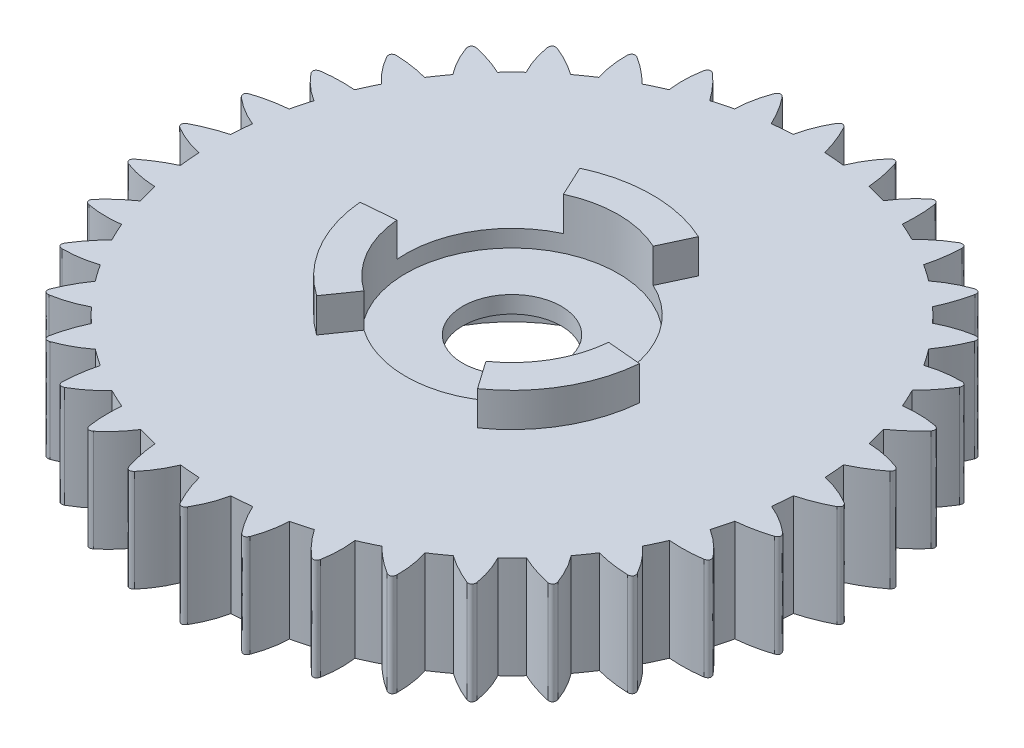
SolidWorks part; units mm, degrees
ref_plane "前视基准面" through (0, 0, 0) normal (0, 0, 1) x (1, 0, 0)
ref_plane "上视基准面" through (0, 0, 0) normal (0, 1, 0) x (1, 0, 0)
ref_plane "右视基准面" through (0, 0, 0) normal (1, 0, 0) x (0, 0, -1)
sketch "草图1" plane through (0, 0, 0) normal (0, 1, 0) x (1, 0, 0)
  circle A0 centre (0, 0) radius 17.5
  dimension "D1" = 35
extrude "凸台-拉伸1" add sketch "草图1" along normal blind 6
sketch "草图2" plane through (0, 0, 0) normal (0, -1, 0) x (1, 0, 0)
  circle A0 centre (0, 0) radius 8
  dimension "D1" = 16
extrude "切除-拉伸1" cut sketch "草图2" against normal blind 4
sketch "草图3" plane through (0, 6, 0) normal (0, 1, 0) x (1, 0, 0)
  circle A0 centre (0, 0) radius 6.25
  dimension "D1" = 12.5
extrude "切除-拉伸2" cut sketch "草图3" against normal blind 1
sketch "草图4" plane through (0, 4, 0) normal (0, -1, 0) x (1, 0, 0)
  circle A0 centre (0, 0) radius 2.9
  dimension "D1" = 5.8
extrude "切除-拉伸3" cut sketch "草图4" against normal blind 10
sketch "草图5" plane through (0, 6, 0) normal (0, 1, 0) x (1, 0, 0)
  line L0 (0, 6.25) -> (0, 12.9088) construction
  line L1 (2.6414, 5.6644) -> (3.4866, 7.477)
  line L2 (-2.6414, 5.6644) -> (-3.4866, 7.477)
  line L3 (3.5849, -5.1197) -> (4.732, -6.758)
  line L4 (6.2262, -0.5447) -> (8.2186, -0.719)
  line L5 (-6.2262, -0.5447) -> (-8.2186, -0.719)
  line L6 (-3.5849, -5.1197) -> (-4.732, -6.758)
  arc A0 (-6.2262, -0.5447) -> (-3.5849, -5.1197) centre (0, 0) ccw
  arc A1 (-8.2186, -0.719) -> (-4.732, -6.758) centre (0, 0) ccw
  arc A2 (3.4866, 7.477) -> (-3.4866, 7.477) centre (0, 0) ccw
  arc A3 (2.6414, 5.6644) -> (-2.6414, 5.6644) centre (0, 0) ccw
  arc A4 (4.732, -6.758) -> (8.2186, -0.719) centre (0, 0) ccw
  arc A5 (3.5849, -5.1197) -> (6.2262, -0.5447) centre (0, 0) ccw
  point P14 (0, 0)
  dimension "D1" = 2
  dimension "D2" = 25
  dimension "D3" = 3
extrude "凸台-拉伸2" add sketch "草图5" along normal blind 2
sketch "草图6" plane through (0, 6, 0) normal (0, 1, 0) x (1, 0, 0)
  line L0 (0, 0) -> (0, 19.4509) construction
  line L1 (1.9956, 17.0765) -> (3.9652, 16.7292)
  line L4 (-1, 17.1636) -> (1, 17.1636)
  line L6 (4.9306, 16.4705) -> (6.81, 15.7865)
  line L7 (7.7158, 15.3641) -> (9.4478, 14.3641)
  line L8 (10.2665, 13.7909) -> (11.7986, 12.5053)
  line L9 (12.5053, 11.7986) -> (13.7909, 10.2665)
  line L10 (14.3641, 9.4478) -> (15.3641, 7.7158)
  line L11 (15.7865, 6.81) -> (16.4705, 4.9306)
  line L12 (16.7292, 3.9652) -> (17.0765, 1.9956)
  line L13 (17.1636, 1) -> (17.1636, -1)
  line L14 (17.0765, -1.9956) -> (16.7292, -3.9652)
  line L15 (16.4705, -4.9306) -> (15.7865, -6.81)
  line L16 (15.3641, -7.7158) -> (14.3641, -9.4478)
  line L17 (13.7909, -10.2665) -> (12.5053, -11.7986)
  line L18 (11.7986, -12.5053) -> (10.2665, -13.7909)
  line L19 (9.4478, -14.3641) -> (7.7158, -15.3641)
  line L20 (6.81, -15.7865) -> (4.9306, -16.4705)
  line L21 (3.9652, -16.7292) -> (1.9956, -17.0765)
  line L22 (1, -17.1636) -> (-1, -17.1636)
  line L23 (-1.9956, -17.0765) -> (-3.9652, -16.7292)
  line L24 (-4.9306, -16.4705) -> (-6.81, -15.7865)
  line L25 (-7.7158, -15.3641) -> (-9.4478, -14.3641)
  line L26 (-10.2665, -13.7909) -> (-11.7986, -12.5053)
  line L27 (-12.5053, -11.7986) -> (-13.7909, -10.2665)
  line L28 (-14.3641, -9.4478) -> (-15.3641, -7.7158)
  line L29 (-15.7865, -6.81) -> (-16.4705, -4.9306)
  line L30 (-16.7292, -3.9652) -> (-17.0765, -1.9956)
  line L31 (-17.1636, -1) -> (-17.1636, 1)
  line L32 (-17.0765, 1.9956) -> (-16.7292, 3.9652)
  line L33 (-16.4705, 4.9306) -> (-15.7865, 6.81)
  line L34 (-15.3641, 7.7158) -> (-14.3641, 9.4478)
  line L35 (-13.7909, 10.2665) -> (-12.5053, 11.7986)
  line L36 (-11.7986, 12.5053) -> (-10.2665, 13.7909)
  line L37 (-9.4478, 14.3641) -> (-7.7158, 15.3641)
  line L38 (-6.81, 15.7865) -> (-4.9306, 16.4705)
  line L39 (-3.9652, 16.7292) -> (-1.9956, 17.0765)
  spline S0 degree 3 poles (-0.2202, 19.3152) (-0.6116, 18.65) (-0.8715, 17.9328) (-1, 17.1636) knots 0.150432 0.150432 0.150432 0.150432 1 1 1 1
  spline S1 degree 3 poles (0.1951, 19.3164) (0.5575, 18.6363) (0.8258, 17.9187) (1, 17.1636) knots 0.146612 0.146612 0.146612 0.146612 1 1 1 1
  spline S2 degree 2 poles (-0.2202, 19.3152) (-0.0056, 19.5865) (0.1951, 19.3164) knots 0 0 0 1 1 1
  spline S3 degree 3 poles (3.1371, 19.06) (2.6363, 18.4728) (2.2558, 17.8117) (1.9956, 17.0765) knots 0.150432 0.150432 0.150432 0.150432 1 1 1 1
  spline S4 degree 3 poles (3.5464, 18.9891) (3.7852, 18.2563) (3.9248, 17.5031) (3.9652, 16.7292) knots 0.146612 0.146612 0.146612 0.146612 1 1 1 1
  spline S5 degree 2 poles (3.1371, 19.06) (3.3956, 19.2899) (3.5464, 18.9891) knots 0 0 0 1 1 1
  spline S6 degree 3 poles (6.3992, 18.2256) (5.804, 17.7344) (5.3144, 17.1494) (4.9306, 16.4705) knots 0.150432 0.150432 0.150432 0.150432 1 1 1 1
  spline S7 degree 3 poles (6.79, 18.0847) (6.8979, 17.3217) (6.9046, 16.5556) (6.81, 15.7865) knots 0.146612 0.146612 0.146612 0.146612 1 1 1 1
  spline S8 degree 2 poles (6.3992, 18.2256) (6.6937, 18.4072) (6.79, 18.0847) knots 0 0 0 1 1 1
  spline S9 degree 3 poles (9.4668, 16.8375) (8.7954, 16.4571) (8.2117, 15.966) (7.7158, 15.3641) knots 0.150432 0.150432 0.150432 0.150432 1 1 1 1
  spline S10 degree 3 poles (9.8272, 16.6309) (9.801, 15.8607) (9.6745, 15.1051) (9.4478, 14.3641) knots 0.146612 0.146612 0.146612 0.146612 1 1 1 1
  spline S11 degree 2 poles (9.4668, 16.8375) (9.7884, 16.9652) (9.8272, 16.6309) knots 0 0 0 1 1 1
  spline S12 degree 3 poles (12.2468, 14.9378) (11.5195, 14.6798) (10.8594, 14.2975) (10.2665, 13.7909) knots 0.150432 0.150432 0.150432 0.150432 1 1 1 1
  spline S13 degree 3 poles (12.5658, 14.6718) (12.4063, 13.9178) (12.1505, 13.1957) (11.7986, 12.5053) knots 0.146612 0.146612 0.146612 0.146612 1 1 1 1
  spline S14 degree 2 poles (12.2468, 14.9378) (12.5856, 15.0077) (12.5658, 14.6718) knots 0 0 0 1 1 1
  spline S15 degree 3 poles (14.6547, 12.5843) (13.8936, 12.4565) (13.1771, 12.1946) (12.5053, 11.7986) knots 0.150432 0.150432 0.150432 0.150432 1 1 1 1
  spline S16 degree 3 poles (14.9226, 12.2669) (14.6346, 11.5521) (14.2573, 10.8853) (13.7909, 10.2665) knots 0.146612 0.146612 0.146612 0.146612 1 1 1 1
  spline S17 degree 2 poles (14.6547, 12.5843) (15.0005, 12.5943) (14.9226, 12.2669) knots 0 0 0 1 1 1
  spline S18 degree 3 poles (16.6173, 9.8483) (15.8456, 9.8546) (15.0945, 9.7211) (14.3641, 9.4478) knots 0.150432 0.150432 0.150432 0.150432 1 1 1 1
  spline S19 degree 3 poles (16.8261, 9.4892) (16.4183, 8.8353) (15.931, 8.2441) (15.3641, 7.7158) knots 0.146612 0.146612 0.146612 0.146612 1 1 1 1
  spline S20 degree 2 poles (16.6173, 9.8483) (16.9596, 9.7981) (16.8261, 9.4892) knots 0 0 0 1 1 1
  spline S21 degree 3 poles (18.075, 6.8131) (17.3161, 6.9534) (16.5533, 6.9523) (15.7865, 6.81) knots 0.150432 0.150432 0.150432 0.150432 1 1 1 1
  spline S22 degree 3 poles (18.2182, 6.4232) (17.7031, 5.8501) (17.1205, 5.3525) (16.4705, 4.9306) knots 0.146612 0.146612 0.146612 0.146612 1 1 1 1
  spline S23 degree 2 poles (18.075, 6.8131) (18.4034, 6.7043) (18.2182, 6.4232) knots 0 0 0 1 1 1
  spline S24 degree 3 poles (18.9835, 3.5709) (18.2604, 3.8408) (17.509, 3.9722) (16.7292, 3.9652) knots 0.150432 0.150432 0.150432 0.150432 1 1 1 1
  spline S25 degree 3 poles (19.0568, 3.1621) (18.45, 2.6871) (17.7899, 2.2983) (17.0765, 1.9956) knots 0.146612 0.146612 0.146612 0.146612 1 1 1 1
  spline S26 degree 2 poles (18.9835, 3.5709) (19.288, 3.4067) (19.0568, 3.1621) knots 0 0 0 1 1 1
  spline S27 degree 3 poles (19.3152, 0.2202) (18.65, 0.6116) (17.9328, 0.8715) (17.1636, 1) knots 0.150432 0.150432 0.150432 0.150432 1 1 1 1
  spline S28 degree 3 poles (19.3164, -0.1951) (18.6363, -0.5575) (17.9187, -0.8258) (17.1636, -1) knots 0.146612 0.146612 0.146612 0.146612 1 1 1 1
  spline S29 degree 2 poles (19.3152, 0.2202) (19.5865, 0.0056) (19.3164, -0.1951) knots 0 0 0 1 1 1
  spline S30 degree 3 poles (19.06, -3.1371) (18.4728, -2.6363) (17.8117, -2.2558) (17.0765, -1.9956) knots 0.150432 0.150432 0.150432 0.150432 1 1 1 1
  spline S31 degree 3 poles (18.9891, -3.5464) (18.2563, -3.7852) (17.5031, -3.9248) (16.7292, -3.9652) knots 0.146612 0.146612 0.146612 0.146612 1 1 1 1
  spline S32 degree 2 poles (19.06, -3.1371) (19.2899, -3.3956) (18.9891, -3.5464) knots 0 0 0 1 1 1
  spline S33 degree 3 poles (18.2256, -6.3992) (17.7344, -5.804) (17.1494, -5.3144) (16.4705, -4.9306) knots 0.150432 0.150432 0.150432 0.150432 1 1 1 1
  spline S34 degree 3 poles (18.0847, -6.79) (17.3217, -6.8979) (16.5556, -6.9046) (15.7865, -6.81) knots 0.146612 0.146612 0.146612 0.146612 1 1 1 1
  spline S35 degree 2 poles (18.2256, -6.3992) (18.4072, -6.6937) (18.0847, -6.79) knots 0 0 0 1 1 1
  spline S36 degree 3 poles (16.8375, -9.4668) (16.4571, -8.7954) (15.966, -8.2117) (15.3641, -7.7158) knots 0.150432 0.150432 0.150432 0.150432 1 1 1 1
  spline S37 degree 3 poles (16.6309, -9.8272) (15.8607, -9.801) (15.1051, -9.6745) (14.3641, -9.4478) knots 0.146612 0.146612 0.146612 0.146612 1 1 1 1
  spline S38 degree 2 poles (16.8375, -9.4668) (16.9652, -9.7884) (16.6309, -9.8272) knots 0 0 0 1 1 1
  spline S39 degree 3 poles (14.9378, -12.2468) (14.6798, -11.5195) (14.2975, -10.8594) (13.7909, -10.2665) knots 0.150432 0.150432 0.150432 0.150432 1 1 1 1
  spline S40 degree 3 poles (14.6718, -12.5658) (13.9178, -12.4063) (13.1957, -12.1505) (12.5053, -11.7986) knots 0.146612 0.146612 0.146612 0.146612 1 1 1 1
  spline S41 degree 2 poles (14.9378, -12.2468) (15.0077, -12.5856) (14.6718, -12.5658) knots 0 0 0 1 1 1
  spline S42 degree 3 poles (12.5843, -14.6547) (12.4565, -13.8936) (12.1946, -13.1771) (11.7986, -12.5053) knots 0.150432 0.150432 0.150432 0.150432 1 1 1 1
  spline S43 degree 3 poles (12.2669, -14.9226) (11.5521, -14.6346) (10.8853, -14.2573) (10.2665, -13.7909) knots 0.146612 0.146612 0.146612 0.146612 1 1 1 1
  spline S44 degree 2 poles (12.5843, -14.6547) (12.5943, -15.0005) (12.2669, -14.9226) knots 0 0 0 1 1 1
  spline S45 degree 3 poles (9.8483, -16.6173) (9.8546, -15.8456) (9.7211, -15.0945) (9.4478, -14.3641) knots 0.150432 0.150432 0.150432 0.150432 1 1 1 1
  spline S46 degree 3 poles (9.4892, -16.8261) (8.8353, -16.4183) (8.2441, -15.931) (7.7158, -15.3641) knots 0.146612 0.146612 0.146612 0.146612 1 1 1 1
  spline S47 degree 2 poles (9.8483, -16.6173) (9.7981, -16.9596) (9.4892, -16.8261) knots 0 0 0 1 1 1
  spline S48 degree 3 poles (6.8131, -18.075) (6.9534, -17.3161) (6.9523, -16.5533) (6.81, -15.7865) knots 0.150432 0.150432 0.150432 0.150432 1 1 1 1
  spline S49 degree 3 poles (6.4232, -18.2182) (5.8501, -17.7031) (5.3525, -17.1205) (4.9306, -16.4705) knots 0.146612 0.146612 0.146612 0.146612 1 1 1 1
  spline S50 degree 2 poles (6.8131, -18.075) (6.7043, -18.4034) (6.4232, -18.2182) knots 0 0 0 1 1 1
  spline S51 degree 3 poles (3.5709, -18.9835) (3.8408, -18.2604) (3.9722, -17.509) (3.9652, -16.7292) knots 0.150432 0.150432 0.150432 0.150432 1 1 1 1
  spline S52 degree 3 poles (3.1621, -19.0568) (2.6871, -18.45) (2.2983, -17.7899) (1.9956, -17.0765) knots 0.146612 0.146612 0.146612 0.146612 1 1 1 1
  spline S53 degree 2 poles (3.5709, -18.9835) (3.4067, -19.288) (3.1621, -19.0568) knots 0 0 0 1 1 1
  spline S54 degree 3 poles (0.2202, -19.3152) (0.6116, -18.65) (0.8715, -17.9328) (1, -17.1636) knots 0.150432 0.150432 0.150432 0.150432 1 1 1 1
  spline S55 degree 3 poles (-0.1951, -19.3164) (-0.5575, -18.6363) (-0.8258, -17.9187) (-1, -17.1636) knots 0.146612 0.146612 0.146612 0.146612 1 1 1 1
  spline S56 degree 2 poles (0.2202, -19.3152) (0.0056, -19.5865) (-0.1951, -19.3164) knots 0 0 0 1 1 1
  spline S57 degree 3 poles (-3.1371, -19.06) (-2.6363, -18.4728) (-2.2558, -17.8117) (-1.9956, -17.0765) knots 0.150432 0.150432 0.150432 0.150432 1 1 1 1
  spline S58 degree 3 poles (-3.5464, -18.9891) (-3.7852, -18.2563) (-3.9248, -17.5031) (-3.9652, -16.7292) knots 0.146612 0.146612 0.146612 0.146612 1 1 1 1
  spline S59 degree 2 poles (-3.1371, -19.06) (-3.3956, -19.2899) (-3.5464, -18.9891) knots 0 0 0 1 1 1
  spline S60 degree 3 poles (-6.3992, -18.2256) (-5.804, -17.7344) (-5.3144, -17.1494) (-4.9306, -16.4705) knots 0.150432 0.150432 0.150432 0.150432 1 1 1 1
  spline S61 degree 3 poles (-6.79, -18.0847) (-6.8979, -17.3217) (-6.9046, -16.5556) (-6.81, -15.7865) knots 0.146612 0.146612 0.146612 0.146612 1 1 1 1
  spline S62 degree 2 poles (-6.3992, -18.2256) (-6.6937, -18.4072) (-6.79, -18.0847) knots 0 0 0 1 1 1
  spline S63 degree 3 poles (-9.4668, -16.8375) (-8.7954, -16.4571) (-8.2117, -15.966) (-7.7158, -15.3641) knots 0.150432 0.150432 0.150432 0.150432 1 1 1 1
  spline S64 degree 3 poles (-9.8272, -16.6309) (-9.801, -15.8607) (-9.6745, -15.1051) (-9.4478, -14.3641) knots 0.146612 0.146612 0.146612 0.146612 1 1 1 1
  spline S65 degree 2 poles (-9.4668, -16.8375) (-9.7884, -16.9652) (-9.8272, -16.6309) knots 0 0 0 1 1 1
  spline S66 degree 3 poles (-12.2468, -14.9378) (-11.5195, -14.6798) (-10.8594, -14.2975) (-10.2665, -13.7909) knots 0.150432 0.150432 0.150432 0.150432 1 1 1 1
  spline S67 degree 3 poles (-12.5658, -14.6718) (-12.4063, -13.9178) (-12.1505, -13.1957) (-11.7986, -12.5053) knots 0.146612 0.146612 0.146612 0.146612 1 1 1 1
  spline S68 degree 2 poles (-12.2468, -14.9378) (-12.5856, -15.0077) (-12.5658, -14.6718) knots 0 0 0 1 1 1
  spline S69 degree 3 poles (-14.6547, -12.5843) (-13.8936, -12.4565) (-13.1771, -12.1946) (-12.5053, -11.7986) knots 0.150432 0.150432 0.150432 0.150432 1 1 1 1
  spline S70 degree 3 poles (-14.9226, -12.2669) (-14.6346, -11.5521) (-14.2573, -10.8853) (-13.7909, -10.2665) knots 0.146612 0.146612 0.146612 0.146612 1 1 1 1
  spline S71 degree 2 poles (-14.6547, -12.5843) (-15.0005, -12.5943) (-14.9226, -12.2669) knots 0 0 0 1 1 1
  spline S72 degree 3 poles (-16.6173, -9.8483) (-15.8456, -9.8546) (-15.0945, -9.7211) (-14.3641, -9.4478) knots 0.150432 0.150432 0.150432 0.150432 1 1 1 1
  spline S73 degree 3 poles (-16.8261, -9.4892) (-16.4183, -8.8353) (-15.931, -8.2441) (-15.3641, -7.7158) knots 0.146612 0.146612 0.146612 0.146612 1 1 1 1
  spline S74 degree 2 poles (-16.6173, -9.8483) (-16.9596, -9.7981) (-16.8261, -9.4892) knots 0 0 0 1 1 1
  spline S75 degree 3 poles (-18.075, -6.8131) (-17.3161, -6.9534) (-16.5533, -6.9523) (-15.7865, -6.81) knots 0.150432 0.150432 0.150432 0.150432 1 1 1 1
  spline S76 degree 3 poles (-18.2182, -6.4232) (-17.7031, -5.8501) (-17.1205, -5.3525) (-16.4705, -4.9306) knots 0.146612 0.146612 0.146612 0.146612 1 1 1 1
  spline S77 degree 2 poles (-18.075, -6.8131) (-18.4034, -6.7043) (-18.2182, -6.4232) knots 0 0 0 1 1 1
  spline S78 degree 3 poles (-18.9835, -3.5709) (-18.2604, -3.8408) (-17.509, -3.9722) (-16.7292, -3.9652) knots 0.150432 0.150432 0.150432 0.150432 1 1 1 1
  spline S79 degree 3 poles (-19.0568, -3.1621) (-18.45, -2.6871) (-17.7899, -2.2983) (-17.0765, -1.9956) knots 0.146612 0.146612 0.146612 0.146612 1 1 1 1
  spline S80 degree 2 poles (-18.9835, -3.5709) (-19.288, -3.4067) (-19.0568, -3.1621) knots 0 0 0 1 1 1
  spline S81 degree 3 poles (-19.3152, -0.2202) (-18.65, -0.6116) (-17.9328, -0.8715) (-17.1636, -1) knots 0.150432 0.150432 0.150432 0.150432 1 1 1 1
  spline S82 degree 3 poles (-19.3164, 0.1951) (-18.6363, 0.5575) (-17.9187, 0.8258) (-17.1636, 1) knots 0.146612 0.146612 0.146612 0.146612 1 1 1 1
  spline S83 degree 2 poles (-19.3152, -0.2202) (-19.5865, -0.0056) (-19.3164, 0.1951) knots 0 0 0 1 1 1
  spline S84 degree 3 poles (-19.06, 3.1371) (-18.4728, 2.6363) (-17.8117, 2.2558) (-17.0765, 1.9956) knots 0.150432 0.150432 0.150432 0.150432 1 1 1 1
  spline S85 degree 3 poles (-18.9891, 3.5464) (-18.2563, 3.7852) (-17.5031, 3.9248) (-16.7292, 3.9652) knots 0.146612 0.146612 0.146612 0.146612 1 1 1 1
  spline S86 degree 2 poles (-19.06, 3.1371) (-19.2899, 3.3956) (-18.9891, 3.5464) knots 0 0 0 1 1 1
  spline S87 degree 3 poles (-18.2256, 6.3992) (-17.7344, 5.804) (-17.1494, 5.3144) (-16.4705, 4.9306) knots 0.150432 0.150432 0.150432 0.150432 1 1 1 1
  spline S88 degree 3 poles (-18.0847, 6.79) (-17.3217, 6.8979) (-16.5556, 6.9046) (-15.7865, 6.81) knots 0.146612 0.146612 0.146612 0.146612 1 1 1 1
  spline S89 degree 2 poles (-18.2256, 6.3992) (-18.4072, 6.6937) (-18.0847, 6.79) knots 0 0 0 1 1 1
  spline S90 degree 3 poles (-16.8375, 9.4668) (-16.4571, 8.7954) (-15.966, 8.2117) (-15.3641, 7.7158) knots 0.150432 0.150432 0.150432 0.150432 1 1 1 1
  spline S91 degree 3 poles (-16.6309, 9.8272) (-15.8607, 9.801) (-15.1051, 9.6745) (-14.3641, 9.4478) knots 0.146612 0.146612 0.146612 0.146612 1 1 1 1
  spline S92 degree 2 poles (-16.8375, 9.4668) (-16.9652, 9.7884) (-16.6309, 9.8272) knots 0 0 0 1 1 1
  spline S93 degree 3 poles (-14.9378, 12.2468) (-14.6798, 11.5195) (-14.2975, 10.8594) (-13.7909, 10.2665) knots 0.150432 0.150432 0.150432 0.150432 1 1 1 1
  spline S94 degree 3 poles (-14.6718, 12.5658) (-13.9178, 12.4063) (-13.1957, 12.1505) (-12.5053, 11.7986) knots 0.146612 0.146612 0.146612 0.146612 1 1 1 1
  spline S95 degree 2 poles (-14.9378, 12.2468) (-15.0077, 12.5856) (-14.6718, 12.5658) knots 0 0 0 1 1 1
  spline S96 degree 3 poles (-12.5843, 14.6547) (-12.4565, 13.8936) (-12.1946, 13.1771) (-11.7986, 12.5053) knots 0.150432 0.150432 0.150432 0.150432 1 1 1 1
  spline S97 degree 3 poles (-12.2669, 14.9226) (-11.5521, 14.6346) (-10.8853, 14.2573) (-10.2665, 13.7909) knots 0.146612 0.146612 0.146612 0.146612 1 1 1 1
  spline S98 degree 2 poles (-12.5843, 14.6547) (-12.5943, 15.0005) (-12.2669, 14.9226) knots 0 0 0 1 1 1
  spline S99 degree 3 poles (-9.8483, 16.6173) (-9.8546, 15.8456) (-9.7211, 15.0945) (-9.4478, 14.3641) knots 0.150432 0.150432 0.150432 0.150432 1 1 1 1
  spline S100 degree 3 poles (-9.4892, 16.8261) (-8.8353, 16.4183) (-8.2441, 15.931) (-7.7158, 15.3641) knots 0.146612 0.146612 0.146612 0.146612 1 1 1 1
  spline S101 degree 2 poles (-9.8483, 16.6173) (-9.7981, 16.9596) (-9.4892, 16.8261) knots 0 0 0 1 1 1
  spline S102 degree 3 poles (-6.8131, 18.075) (-6.9534, 17.3161) (-6.9523, 16.5533) (-6.81, 15.7865) knots 0.150432 0.150432 0.150432 0.150432 1 1 1 1
  spline S103 degree 3 poles (-6.4232, 18.2182) (-5.8501, 17.7031) (-5.3525, 17.1205) (-4.9306, 16.4705) knots 0.146612 0.146612 0.146612 0.146612 1 1 1 1
  spline S104 degree 2 poles (-6.8131, 18.075) (-6.7043, 18.4034) (-6.4232, 18.2182) knots 0 0 0 1 1 1
  spline S105 degree 3 poles (-3.5709, 18.9835) (-3.8408, 18.2604) (-3.9722, 17.509) (-3.9652, 16.7292) knots 0.150432 0.150432 0.150432 0.150432 1 1 1 1
  spline S106 degree 3 poles (-3.1621, 19.0568) (-2.6871, 18.45) (-2.2983, 17.7899) (-1.9956, 17.0765) knots 0.146612 0.146612 0.146612 0.146612 1 1 1 1
  spline S107 degree 2 poles (-3.5709, 18.9835) (-3.4067, 19.288) (-3.1621, 19.0568) knots 0 0 0 1 1 1
  point P257 (0, 0)
  dimension "D1" = 36
extrude "凸台-拉伸3" add sketch "草图6" against normal blind 6
